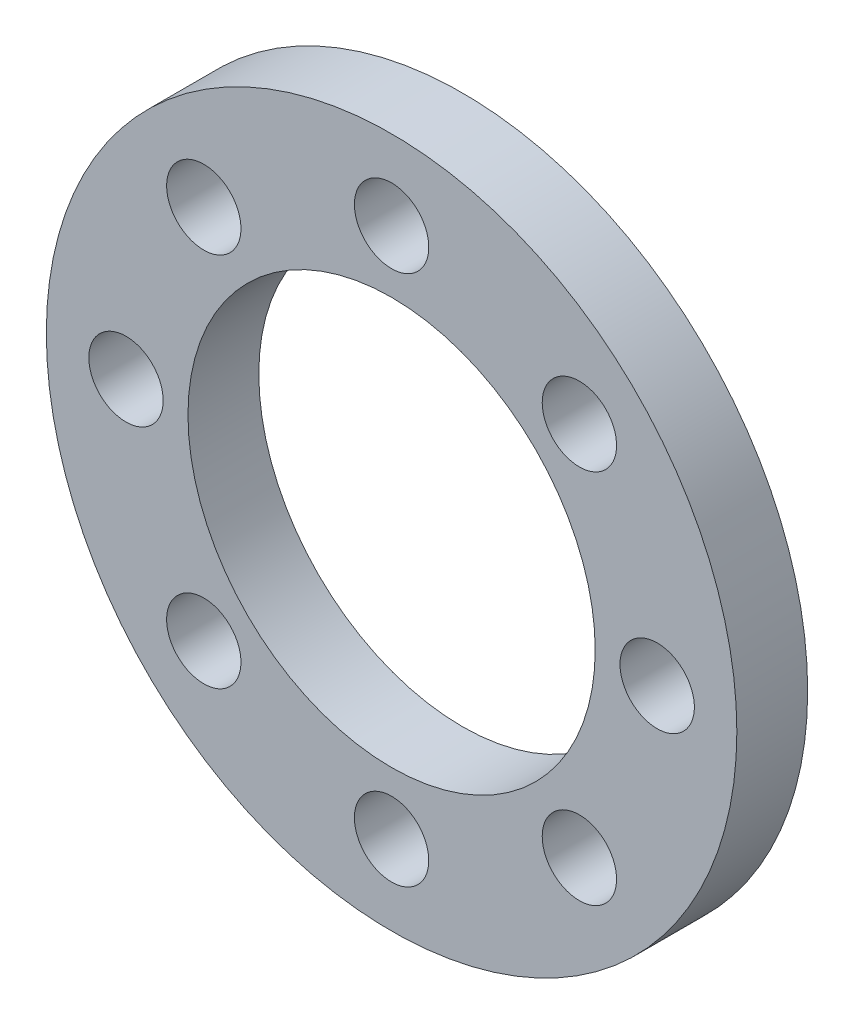
SolidWorks part; units mm, degrees
material "Copper"
ref_plane "Front Plane" through (0, 0, 0) normal (0, 0, 1) x (1, 0, 0)
ref_plane "Top Plane" through (0, 0, 0) normal (0, 1, 0) x (1, 0, 0)
ref_plane "Right Plane" through (0, 0, 0) normal (1, 0, 0) x (0, 0, -1)
sketch "Sketch2" plane through (0, 0, 0) normal (0, 0, 1) x (1, 0, 0)
  circle A0 centre (0, 0) radius 9.75
  circle A1 centre (0, 0) radius 5.75
  dimension "D1" = 19.5
  dimension "D2" = 11.5
extrude "Boss-Extrude1" add sketch "Sketch2" along normal blind 2
sketch "Sketch4" plane through (0, 0, 0) normal (0, 0, -1) x (-1, 0, 0)
  circle A0 centre (0, 0) radius 7.5 construction
  circle A1 centre (0, 7.5) radius 1.05
  circle A2 centre (5.3033, 5.3033) radius 1.05
  circle A3 centre (7.5, 0) radius 1.05
  circle A4 centre (5.3033, -5.3033) radius 1.05
  circle A5 centre (0, -7.5) radius 1.05
  circle A6 centre (-5.3033, -5.3033) radius 1.05
  circle A7 centre (-7.5, 0) radius 1.05
  circle A8 centre (-5.3033, 5.3033) radius 1.05
  point P21 (0, 0)
  dimension "D1" = 8
extrude "Cut-Extrude1" cut sketch "Sketch4" against normal through all
